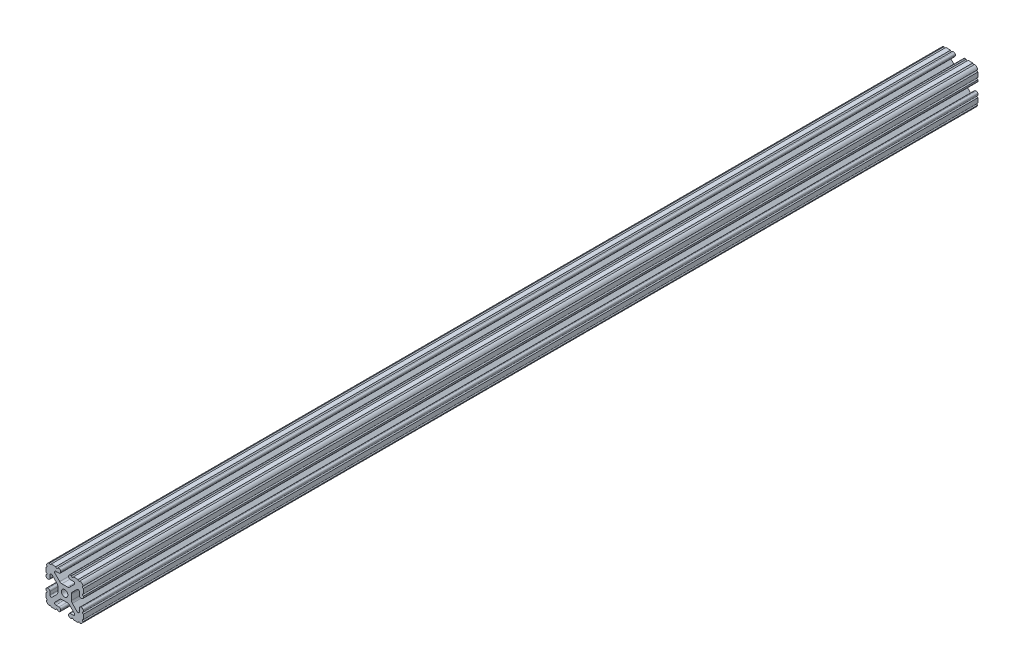
SolidWorks part; units mm, degrees
ref_plane "Front Plane" through (0, 0, 0) normal (0, 0, 1) x (1, 0, 0)
ref_plane "Top Plane" through (0, 0, 0) normal (0, 1, 0) x (1, 0, 0)
ref_plane "Right Plane" through (0, 0, 0) normal (1, 0, 0) x (0, 0, -1)
sketch "Sketch2" plane through (0, 0, 0) normal (0, 0, 1) x (1, 0, 0)
  line L0 (0, 19.05) -> (0, -19.05) construction
  line L1 (-19.05, 0) -> (19.05, 0) construction
  line L2 (4.064, -19.05) -> (19.05, -19.05)
  line L3 (19.05, -19.05) -> (19.05, -4.064)
  line L4 (4.064, -19.05) -> (4.064, -14.986)
  line L5 (4.064, -14.986) -> (12.1123, -14.986)
  line L6 (12.1123, -14.986) -> (4.1113, -6.985)
  line L7 (0, 0) -> (19.05, -19.05) construction
  line L8 (19.05, -4.064) -> (14.986, -4.064)
  line L9 (14.986, -4.064) -> (14.986, -12.1123)
  line L10 (14.986, -12.1123) -> (6.985, -4.1113)
  circle A0 centre (0, 0) radius 3.3274
  arc A1 (8.9963, -14.986) -> (9.909, -12.7826) centre (8.9963, -13.6953) ccw construction
  point P8 (0, -6.985)
  dimension "Center Hole Diameter" = 6.6548
  dimension "Rail Height" = 38.1
  dimension "Rail Width" = 38.1
  dimension "T-Slot Width" = 8.128
  dimension "Slot Inner Width" = 20.574
  dimension "Thickness" = 4.064
  dimension "Slot Depth" = 8.001
  dimension "D1" = 4.064
sketch "Sketch3" plane through (0, 0, 0) normal (1, 0, 0) x (0, 0, -1)
  line L0 (-457.2, -19.05) -> (457.2, -19.05) construction
  line L1 (-431.8, 0) -> (431.8, 0) construction
  dimension "Length" = 914.4
  dimension "D1" = 25.4
sketch "Sketch4" plane through (0, 0, 0) normal (0, 0, 1) x (1, 0, 0)
  line L0 (5.7912, -19.05) -> (14.3002, -19.05)
  line L1 (4.064, -19.05) -> (19.05, -19.05) construction
  line L2 (4.064, -19.05) -> (4.064, -14.986) construction
  line L3 (4.064, -14.986) -> (12.1123, -14.986) construction
  line L4 (4.064, -16.7132) -> (4.064, -17.3228)
  line L5 (5.7912, -14.986) -> (8.9963, -14.986)
  line L6 (0, -6.985) -> (2.833, -6.985)
  line L7 (12.1123, -14.986) -> (4.1113, -6.985) construction
  line L8 (5.0152, -7.8889) -> (9.909, -12.7826)
  line L9 (19.05, -19.05) -> (19.05, -4.064) construction
  line L10 (14.986, -12.1123) -> (6.985, -4.1113) construction
  line L11 (14.986, -4.064) -> (14.986, -12.1123) construction
  line L12 (14.986, -8.9963) -> (14.986, -5.7912)
  line L13 (19.05, -4.064) -> (14.986, -4.064) construction
  line L14 (16.7132, -4.064) -> (17.3228, -4.064)
  line L15 (19.05, -5.7912) -> (19.05, -14.3002)
  line L16 (12.7826, -9.909) -> (7.8889, -5.0152)
  line L17 (6.985, 0) -> (6.985, -2.833)
  line L18 (-19.05, 0) -> (19.05, 0) construction
  line L19 (0, -6.985) -> (0, -3.3274)
  line L20 (0, 19.05) -> (0, -19.05) construction
  line L21 (6.985, 0) -> (3.3274, 0)
  arc A0 (4.064, -17.3228) -> (5.7912, -19.05) centre (5.7912, -17.3228) ccw
  arc A2 (4.064, -16.7132) -> (5.7912, -14.986) centre (5.7912, -16.7132) cw
  arc A3 (8.9963, -14.986) -> (9.909, -12.7826) centre (8.9963, -13.6953) ccw
  arc A4 (2.833, -6.985) -> (5.0152, -7.8889) centre (2.833, -10.0711) cw
  arc A5 (14.3002, -19.05) -> (19.05, -14.3002) centre (14.3002, -14.3002) ccw
  arc A6 (12.7826, -9.909) -> (14.986, -8.9963) centre (13.6953, -8.9963) ccw
  arc A7 (14.986, -5.7912) -> (16.7132, -4.064) centre (16.7132, -5.7912) cw
  arc A8 (17.3228, -4.064) -> (19.05, -5.7912) centre (17.3228, -5.7912) cw
  arc A9 (7.8889, -5.0152) -> (6.985, -2.833) centre (10.0711, -2.833) cw
  circle A10 centre (0, 0) radius 3.3274 construction
  arc A11 (0, -3.3274) -> (3.3274, 0) centre (0, 0) ccw
  dimension "D1" = 4.7498
  dimension "D2" = 3.0861
  dimension "D3" = 1.7272
extrude "Boss-Extrude1" add sketch "Sketch4" along normal mid plane 914.4
sketch "Sketch5" plane through (0, 0, 0) normal (0, 0, 1) x (1, 0, 0)
  line L0 (4.064, -19.05) -> (19.05, -19.05) construction
  line L1 (5.7912, -14.986) -> (8.9963, -14.986) construction
  line L3 (0, 0) -> (19.05, -19.05) construction
  line L4 (8.9963, -14.986) -> (8.9963, -19.05) construction
  line L5 (12.1123, -14.986) -> (4.1113, -6.985) construction
  circle A0 centre (14.7395, -19.05) radius 1.016
  circle A1 centre (7.9803, -19.05) radius 1.016
  circle A2 centre (19.05, -14.7395) radius 1.016
  circle A3 centre (19.05, -7.9803) radius 1.016
  point P10 (7.3938, -14.986)
  point P12 (13.6953, -8.9963)
  dimension "D1" = 2.032
extrude "Cut-Extrude1" cut sketch "Sketch5" against normal through all both and the other way through all
mirror "Mirror1" about plane through (0, 0, 0) normal (1, 0, 0) of bodies 137 134
mirror "Mirror2" about plane through (0, 0, 0) normal (0, 1, 0) of bodies 135
equation "\"D1@Boss-Extrude1\"=\"Length@Sketch3\""
equation "\"D1@Sketch2\"=\"Thickness@Sketch2\""
equation "\"D2@Sketch4\"=\"Slot Inner Width@Sketch2\"*0.15"
equation "\"D1@Sketch4\"=\"D3@Sketch4\"*2.75"
equation "\"D3@Sketch4\"=\"Thickness@Sketch2\"*0.425"
equation "\"D1@Sketch5\"=\"Thickness@Sketch2\"*0.5"
